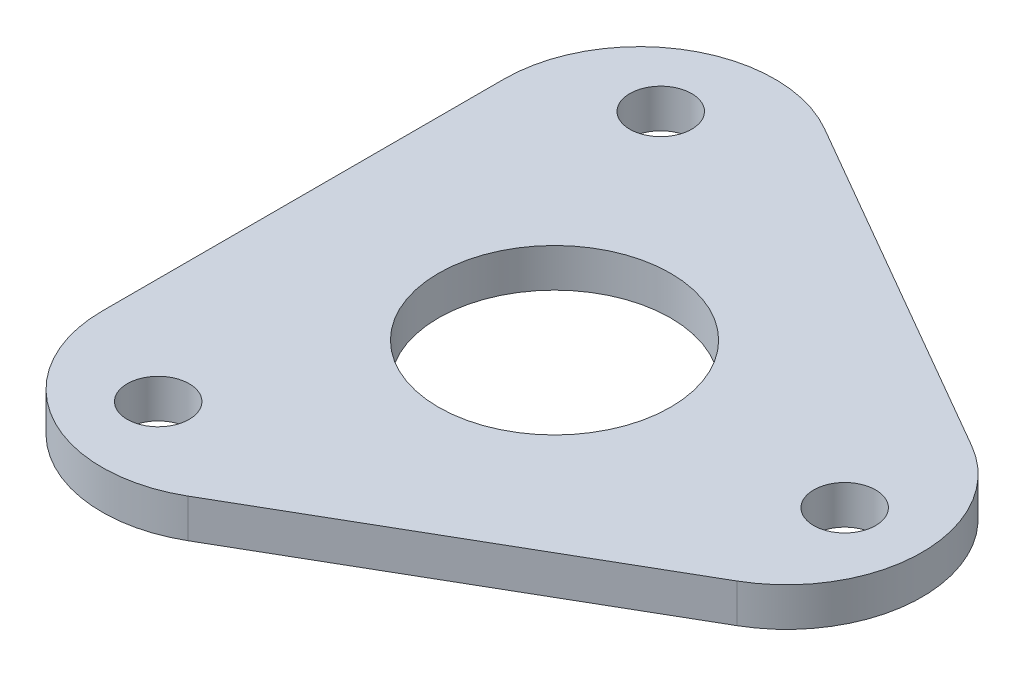
SolidWorks part; units mm, degrees
ref_plane "Front Plane" through (0, 0, 0) normal (0, 0, 1) x (1, 0, 0)
ref_plane "Top Plane" through (0, 0, 0) normal (0, 1, 0) x (1, 0, 0)
ref_plane "Right Plane" through (0, 0, 0) normal (1, 0, 0) x (0, 0, -1)
sketch "Sketch1" plane through (0, 0, 0) normal (0, 1, 0) x (1, 0, 0)
  line L0 (0, 0) -> (-13, 22.5167) construction
  line L1 (26, 0) -> (-13, 22.5167)
  line L2 (-13, 22.5167) -> (-13, -22.5167)
  line L3 (-13, -22.5167) -> (26, 0)
  circle A0 centre (0, 0) radius 13 construction
  circle A1 centre (-7.5, 12.9904) radius 1.6
  circle A2 centre (15, 0) radius 1.6
  circle A3 centre (-7.5, -12.9904) radius 1.6
  circle A4 centre (0, 0) radius 6
  point P15 (0, 0)
  dimension "D1" = 26
  dimension "D2" = 3.2
  dimension "D3" = 15
  dimension "D5" = 12
  dimension "D4" = 3
extrude "Boss-Extrude1" add sketch "Sketch1" along normal blind 2
fillet "Fillet1" radius 7 3 edges at (-13, 1, -22.5167) (-13, 1, 22.5167) (26, 1, 0)
